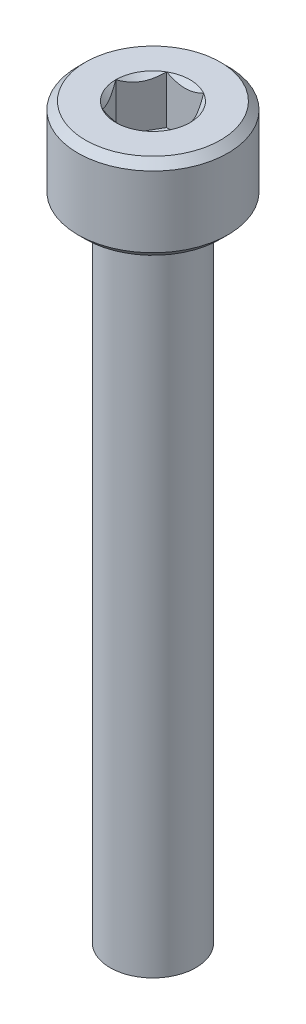
SolidWorks part; units mm, degrees
ref_plane "Front" through (0, 0, 0) normal (0, 0, 1) x (1, 0, 0)
ref_plane "Top" through (0, 0, 0) normal (0, 1, 0) x (1, 0, 0)
ref_plane "Right" through (0, 0, 0) normal (1, 0, 0) x (0, 0, -1)
sketch "Sketch1" plane through (0, 0, 0) normal (0, 1, 0) x (1, 0, 0)
  circle A0 centre (0, 0) radius 3.5
  dimension "D1" = 7
extrude "Boss-Extrude1" add sketch "Sketch1" along normal blind 4
sketch "Sketch2" plane through (0, 4, 0) normal (0, 1, 0) x (1, 0, 0)
  line L1 (0.866, 1.5) -> (-0.866, 1.5)
  line L2 (-0.866, 1.5) -> (-1.7321, 0)
  line L3 (-1.7321, 0) -> (-0.866, -1.5)
  line L4 (-0.866, -1.5) -> (0.866, -1.5)
  line L5 (0.866, -1.5) -> (1.7321, 0)
  line L6 (1.7321, 0) -> (0.866, 1.5)
  circle A0 centre (0, 0) radius 1.5 construction
  point P10 (0, 1.5)
  dimension "D1" = 3
extrude "Cut-Extrude1" cut sketch "Sketch2" against normal blind 2.25
sketch "Sketch3" plane through (0, 4, 0) normal (0, 1, 0) x (1, 0, 0)
  circle A0 centre (0, 0) radius 1.7321
extrude "Cut-Extrude2" cut sketch "Sketch3" against normal through all draft 45
chamfer "Chamfer1" distance 0.35 angle 45 2 edges at (0, 0, 3.5) (0, 4, 3.5)
sketch "草图1" plane through (0, 0, 0) normal (0, -1, 0) x (-1, 0, 0)
  circle A0 centre (0, 0) radius 2
  dimension "D1" = 4
extrude "凸台-拉伸1" add sketch "草图1" along normal blind 30
